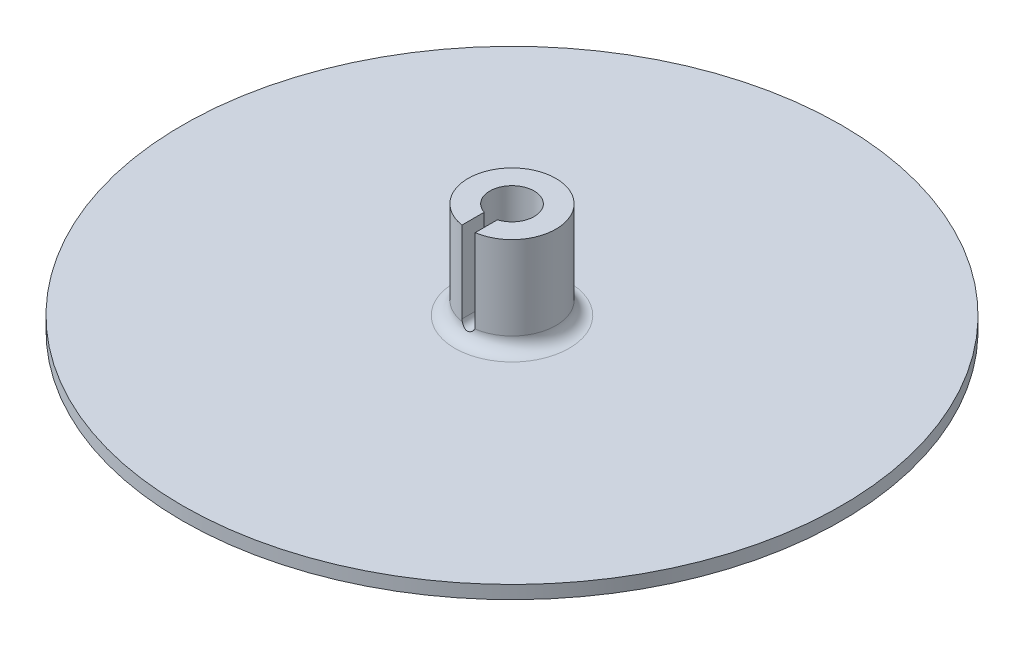
SolidWorks part; units mm, degrees
ref_plane "Front Plane" through (0, 0, 0) normal (0, 0, 1) x (1, 0, 0)
ref_plane "Top Plane" through (0, 0, 0) normal (0, 1, 0) x (1, 0, 0)
ref_plane "Right Plane" through (0, 0, 0) normal (1, 0, 0) x (0, 0, -1)
sketch "Sketch1" plane through (0, 0, 0) normal (0, 1, 0) x (1, 0, 0)
  circle A0 centre (0, 0) radius 75
  dimension "D1" = 150
extrude "Boss-Extrude1" add sketch "Sketch1" along normal blind 3
sketch "Sketch2" plane through (0, 3, 0) normal (0, 1, 0) x (1, 0, 0)
  circle A0 centre (0, 0) radius 10
  circle A1 centre (0, 0) radius 5.05
  dimension "D1" = 10.1
  dimension "D2" = 20
extrude "Boss-Extrude2" add sketch "Sketch2" along normal blind 22
fillet "Fillet1" radius 3 1 edges at (0, 3, 10)
sketch "Sketch3" plane through (0, 0, 0) normal (0, 0, 1) x (1, 0, 0)
  line L0 (0, 25) -> (0, 6.5) construction
  line L1 (1.5, 25) -> (1.5, 6.5)
  line L2 (-1.5, 25) -> (-1.5, 6.5)
  line L3 (13, 3) -> (-13, 3) construction
  line L4 (5.05, 25) -> (-5.05, 25) construction
  arc A0 (1.5, 25) -> (-1.5, 25) centre (0, 25) ccw
  arc A1 (-1.5, 6.5) -> (1.5, 6.5) centre (0, 6.5) ccw
  point P3 (0, 15.75)
  point P10 (0, 0)
  dimension "D1" = 2
  dimension "D2" = 3
extrude "Cut-Extrude1" cut sketch "Sketch3" along normal through all
hole_wizard "CSK for M3 Hex Socket Countersunk Head Screw1" positions "Sketch4" profile "Sketch5" countersink size "M3" standard "DIN" end condition through all
sketch "Sketch4" plane through (0, 0, 0) normal (0, -1, 0) x (-1, 0, 0)
  point P0 (0, 0)
sketch "Sketch5" plane through (0, 0, 0) normal (1, 0, 0) x (0, 0, -1)
  line L0 (0, 0) -> (0, 25)
  line L1 (0, 25) -> (1.8, 25)
  line L2 (1.8, 25) -> (1.8, 1.67)
  line L3 (1.8, 1.67) -> (3.47, 0)
  line L5 (3.47, 0) -> (0, 0)
  line L6 (-1.8, 1.67) -> (-3.47, 0) construction
  line L11 (0, -6.35) -> (0, 107.95) construction
  dimension "Thru Hole Dia." = 3.6
  dimension "Thru Hole Depth" = 25
  dimension "Near C'Sink Dia." = 6.94
  dimension "Near C'Sink Angle" = 90
